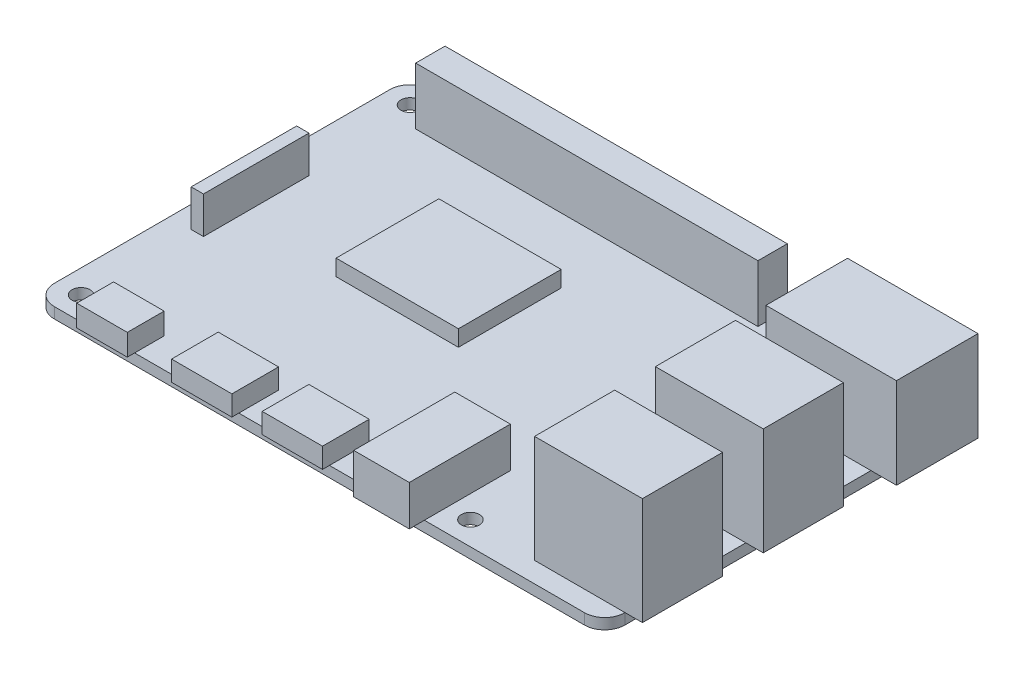
SolidWorks part; units mm, degrees
ref_plane "Front Plane" through (0, 0, 0) normal (0, 0, 1) x (1, 0, 0)
ref_plane "Top Plane" through (0, 0, 0) normal (0, 1, 0) x (1, 0, 0)
ref_plane "Right Plane" through (0, 0, 0) normal (1, 0, 0) x (0, 0, -1)
sketch "Sketch1" plane through (0, 0, 0) normal (0, 1, 0) x (1, 0, 0)
  line L1 (-39.5, -28) -> (39.5, -28)
  line L2 (-42.5, -25) -> (-42.5, 25)
  line L3 (-39.5, 28) -> (39.5, 28)
  line L4 (42.5, -25) -> (42.5, 25)
  line L5 (-42.5, -28) -> (42.5, 28) construction
  line L6 (-42.5, 28) -> (42.5, -28) construction
  arc A0 (39.5, 28) -> (42.5, 25) centre (39.5, 25) cw
  arc A1 (42.5, -25) -> (39.5, -28) centre (39.5, -25) cw
  arc A2 (-39.5, -28) -> (-42.5, -25) centre (-39.5, -25) cw
  arc A3 (-39.5, 28) -> (-42.5, 25) centre (-39.5, 25) ccw
  circle A8 centre (-39, 24.5) radius 1.35
  circle A9 centre (19, 24.5) radius 1.35
  circle A10 centre (19, -24.5) radius 1.35
  circle A11 centre (-39, -24.5) radius 1.35
  point P0 (0, 0)
  dimension "D3" = 3
  dimension "D4" = 3.5
  dimension "D5" = 3.5
  dimension "D6" = 2.7
  dimension "D1" = 85
  dimension "D2" = 56
  dimension "D7" = 2
  dimension "D8" = 2
extrude "Boss-Extrude1" add sketch "Sketch1" along normal blind 1.6
sketch "Sketch2" plane through (0, 1.6, 0) normal (0, 1, 0) x (1, 0, 0)
  line L0 (-42.5, 25) -> (-42.5, -25) construction
  line L1 (-35.0666, -29.0872) -> (-27.5334, -29.0872)
  line L2 (-35.0666, -29.0872) -> (-35.0666, -23.6005)
  line L3 (-35.0666, -23.6005) -> (-27.5334, -23.6005)
  line L4 (-27.5334, -29.0872) -> (-27.5334, -23.6005)
  line L5 (-35.0666, -29.0872) -> (-27.5334, -23.6005) construction
  line L6 (-35.0666, -23.6005) -> (-27.5334, -29.0872) construction
  point P0 (-31.3, -26.3438)
  dimension "D1" = 11.2
extrude "Boss-Extrude2" add sketch "Sketch2" along normal blind 3.2
sketch "Sketch3" plane through (0, 1.6, 0) normal (0, 1, 0) x (1, 0, 0)
  line L0 (-42.5, 25) -> (-42.5, -25) construction
  line L1 (-20.993, -29.0343) -> (-12.007, -29.0343)
  line L2 (-20.993, -29.0343) -> (-20.993, -22.0773)
  line L3 (-20.993, -22.0773) -> (-12.007, -22.0773)
  line L4 (-12.007, -29.0343) -> (-12.007, -22.0773)
  line L5 (-20.993, -29.0343) -> (-12.007, -22.0773) construction
  line L6 (-20.993, -22.0773) -> (-12.007, -29.0343) construction
  line L7 (-7.493, -29.0343) -> (1.493, -29.0343)
  line L8 (-7.493, -29.0343) -> (-7.493, -22.0773)
  line L9 (-7.493, -22.0773) -> (1.493, -22.0773)
  line L10 (1.493, -29.0343) -> (1.493, -22.0773)
  line L11 (-7.493, -29.0343) -> (1.493, -22.0773) construction
  line L12 (-7.493, -22.0773) -> (1.493, -29.0343) construction
  line L13 (-3, -25.5558) -> (-16.5, -25.5558) construction
  point P0 (-16.5, -25.5558)
  point P5 (-3, -25.5558)
  dimension "D1" = 26
  dimension "D2" = 13.5
extrude "Boss-Extrude3" add sketch "Sketch3" along normal blind 3
sketch "Sketch4" plane through (0, 1.6, 0) normal (0, 1, 0) x (1, 0, 0)
  line L0 (-42.5, 25) -> (-42.5, -25) construction
  line L1 (7.3597, -30.2486) -> (15.6403, -30.2486)
  line L2 (7.3597, -30.2486) -> (7.3597, -15.1929)
  line L3 (7.3597, -15.1929) -> (15.6403, -15.1929)
  line L4 (15.6403, -30.2486) -> (15.6403, -15.1929)
  line L5 (7.3597, -30.2486) -> (15.6403, -15.1929) construction
  line L6 (7.3597, -15.1929) -> (15.6403, -30.2486) construction
  point P0 (11.5, -22.7208)
  dimension "D1" = 54
extrude "Boss-Extrude4" add sketch "Sketch4" along normal blind 6
sketch "Sketch5" plane through (0, 1.6, 0) normal (0, 1, 0) x (1, 0, 0)
  line L0 (15.6403, -28) -> (39.5, -28) construction
  line L1 (29.0258, -24.9694) -> (45.0958, -24.9694)
  line L2 (29.0258, -24.9694) -> (29.0258, -13.0306)
  line L3 (29.0258, -13.0306) -> (45.0958, -13.0306)
  line L4 (45.0958, -24.9694) -> (45.0958, -13.0306)
  line L5 (29.0258, -24.9694) -> (45.0958, -13.0306) construction
  line L6 (29.0258, -13.0306) -> (45.0958, -24.9694) construction
  line L7 (29.0258, -6.9694) -> (45.0958, -6.9694)
  line L8 (29.0258, -6.9694) -> (29.0258, 4.9694)
  line L9 (29.0258, 4.9694) -> (45.0958, 4.9694)
  line L10 (45.0958, -6.9694) -> (45.0958, 4.9694)
  line L11 (29.0258, -6.9694) -> (45.0958, 4.9694) construction
  line L12 (29.0258, 4.9694) -> (45.0958, -6.9694) construction
  line L13 (37.0608, -19) -> (37.0608, -1) construction
  point P0 (37.0608, -19)
  point P5 (37.0608, -1)
  dimension "D1" = 9
  dimension "D2" = 27
extrude "Boss-Extrude5" add sketch "Sketch5" along normal blind 16
sketch "Sketch6" plane through (0, 1.6, 0) normal (0, 1, 0) x (1, 0, 0)
  line L0 (15.6403, -28) -> (39.5, -28) construction
  line L1 (26.8544, 11.6748) -> (46.2951, 11.6748)
  line L2 (26.8544, 11.6748) -> (26.8544, 23.8252)
  line L3 (26.8544, 23.8252) -> (46.2951, 23.8252)
  line L4 (46.2951, 11.6748) -> (46.2951, 23.8252)
  line L5 (26.8544, 11.6748) -> (46.2951, 23.8252) construction
  line L6 (26.8544, 23.8252) -> (46.2951, 11.6748) construction
  point P0 (36.5748, 17.75)
  dimension "D1" = 45.75
extrude "Boss-Extrude6" add sketch "Sketch6" along normal blind 13.5
sketch "Sketch7" plane through (0, 1.6, 0) normal (0, 1, 0) x (1, 0, 0)
  line L0 (-12.007, -28) -> (-7.493, -28) construction
  line L1 (-22.3628, 12.1548) -> (-4.1372, 12.1548)
  line L2 (-22.3628, 12.1548) -> (-22.3628, -3.1548)
  line L3 (-22.3628, -3.1548) -> (-4.1372, -3.1548)
  line L4 (-4.1372, 12.1548) -> (-4.1372, -3.1548)
  line L5 (-22.3628, 12.1548) -> (-4.1372, -3.1548) construction
  line L6 (-22.3628, -3.1548) -> (-4.1372, 12.1548) construction
  line L7 (-42.5, 25) -> (-42.5, -25) construction
  point P0 (-13.25, 4.5)
  dimension "D1" = 32.5
  dimension "D2" = 29.25
extrude "Boss-Extrude7" add sketch "Sketch7" along normal blind 2.4
sketch "Sketch8" plane through (0, 1.6, 0) normal (0, 1, 0) x (1, 0, 0)
  line L0 (-42.5, 25) -> (-42.5, -25) construction
  line L1 (-35.4993, 26.2128) -> (15.4993, 26.2128)
  line L2 (-35.4993, 26.2128) -> (-35.4993, 21.8371)
  line L3 (-35.4993, 21.8371) -> (15.4993, 21.8371)
  line L4 (15.4993, 26.2128) -> (15.4993, 21.8371)
  line L5 (-35.4993, 26.2128) -> (15.4993, 21.8371) construction
  line L6 (-35.4993, 21.8371) -> (15.4993, 26.2128) construction
  point P0 (-10, 24.025)
  dimension "D1" = 32.5
extrude "Boss-Extrude8" add sketch "Sketch8" along normal blind 8.5
sketch "Sketch9" plane through (0, 1.6, 0) normal (0, 1, 0) x (1, 0, 0)
  line L0 (39.5, 28) -> (-39.5, 28) construction
  line L1 (-39.248, -7.8596) -> (-37.4166, -7.8596)
  line L2 (-39.248, -7.8596) -> (-39.248, 7.8596)
  line L3 (-39.248, 7.8596) -> (-37.4166, 7.8596)
  line L4 (-37.4166, -7.8596) -> (-37.4166, 7.8596)
  line L5 (-39.248, -7.8596) -> (-37.4166, 7.8596) construction
  line L6 (-39.248, 7.8596) -> (-37.4166, -7.8596) construction
  point P0 (-38.3323, 0)
  dimension "D1" = 28
extrude "Boss-Extrude9" add sketch "Sketch9" along normal blind 5.5
